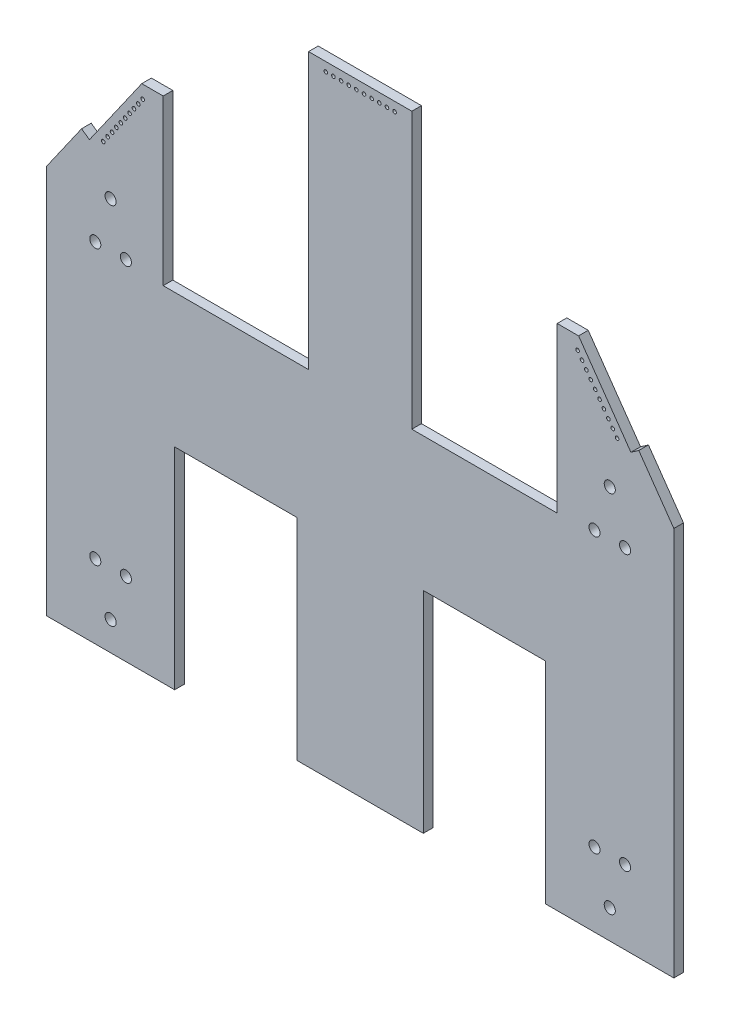
SolidWorks part; units mm, degrees
ref_plane "Front Plane" through (0, 0, 0) normal (0, 0, 1) x (1, 0, 0)
ref_plane "Top Plane" through (0, 0, 0) normal (0, 1, 0) x (1, 0, 0)
ref_plane "Right Plane" through (0, 0, 0) normal (1, 0, 0) x (0, 0, -1)
sketch "Sketch1" plane through (0, 0, 0) normal (0, 0, 1) x (1, 0, 0)
  line L0 (-19.3675, 84.4165) -> (-15.8104, 84.4165)
  line L1 (-5.817, 72.934) -> (-7.1277, 72.0162)
  line L2 (-5.817, 72.934) -> (0, 64.6264)
  line L3 (-15.8104, 84.4165) -> (-7.1277, 72.0162)
  line L4 (-62.5475, 0) -> (-62.5475, 34.925)
  line L5 (-62.5475, 34.925) -> (-82.8675, 34.925)
  line L6 (-82.8675, 34.925) -> (-82.8675, 0)
  line L7 (-21.2725, 34.925) -> (-21.2725, 0)
  line L8 (-41.5925, 34.925) -> (-21.2725, 34.925)
  line L9 (-41.5925, 0) -> (-41.5925, 34.925)
  line L10 (-82.8675, 0) -> (-104.14, 0)
  line L11 (-41.5925, 0) -> (-62.5475, 0)
  line L12 (-84.7725, 84.4165) -> (-84.7725, 57.15)
  line L13 (-84.7725, 57.15) -> (-60.6425, 57.15)
  line L14 (-60.6425, 57.15) -> (-60.6425, 102.87)
  line L18 (-43.4975, 102.87) -> (-60.6425, 102.87)
  line L24 (-43.4975, 102.87) -> (-43.4975, 57.15)
  line L25 (-43.4975, 57.15) -> (-19.3675, 57.15)
  line L26 (-19.3675, 57.15) -> (-19.3675, 84.4165)
  line L95 (0, 0) -> (0, 64.6264)
  line L96 (-104.14, 0) -> (-104.14, 64.6264)
  line L97 (0, 0) -> (-21.2725, 0)
  line L98 (-88.3296, 84.4165) -> (-97.0123, 72.0162)
  line L99 (-84.7725, 84.4165) -> (-88.3296, 84.4165)
  line L100 (-98.323, 72.934) -> (-97.0123, 72.0162)
  line L101 (-98.323, 72.934) -> (-104.14, 64.6264)
  line L299 (-52.07, 102.87) -> (-52.07, 0) construction
  dimension "D2" = 21.2725
  dimension "D5" = 104.14
  dimension "D6" = 82.8675
  dimension "D7" = 34.925
  dimension "D8" = 145
  dimension "D9" = 5.817
  dimension "D10" = 1.6
  dimension "D3" = 41.5925
  dimension "D4" = 62.5475
  dimension "D11" = 7.1277
  dimension "D12" = 15.8104
  dimension "D13" = 19.3675
  dimension "D14" = 19.3675
  dimension "D15" = 43.4975
  dimension "D16" = 57.15
  dimension "D17" = 84.4165
  dimension "D18" = 72.0162
  dimension "D19" = 72.934
  dimension "D20" = 64.6264
  dimension "D21" = 102.87
extrude "Boss-Extrude1" add sketch "Sketch1" along normal blind 1.6
sketch "Sketch2" plane through (0, 0, 0) normal (0, 0, -1) x (-1, 0, 0)
  line L1 (62.1596, 26.0248) -> (-24.5974, 26.0248)
  line L2 (62.1596, 26.0248) -> (62.1596, 63.281)
  line L3 (62.1596, 63.281) -> (-24.5974, 63.281)
  line L4 (-24.5974, 26.0248) -> (-24.5974, 63.281)
  arc A0 (-27.1374, 26.0248) -> (-24.5974, 23.4848) centre (-24.5974, 26.0248) ccw construction
ref_plane "Plane1" through (-52.07, 0, 0) normal (-1, 0, 0) x (0, 0, 1)
sketch "Sketch3" plane through (0, 0, 1.6) normal (0, 0, 1) x (1, 0, 0)
  line L0 (-92.7164, 4.9421) -> (-94.2912, 4.6373) construction
  line L1 (-94.2912, 4.9421) -> (-92.7164, 4.6373) construction
  line L2 (-95.2564, 12.4097) -> (-96.8312, 12.1049) construction
  line L3 (-96.8312, 12.4097) -> (-95.2564, 12.1049) construction
  line L4 (-92.7164, 4.9421) -> (-94.2912, 4.9421)
  line L5 (-92.7164, 4.6373) -> (-92.7164, 4.9421)
  line L6 (-94.2912, 4.6373) -> (-92.7164, 4.6373)
  line L7 (-94.2912, 4.9421) -> (-94.2912, 4.6373)
  line L8 (-92.7164, 4.9421) -> (-94.2912, 4.9421)
  line L9 (-92.7164, 4.6373) -> (-92.7164, 4.9421)
  line L10 (-94.2912, 4.6373) -> (-92.7164, 4.6373)
  line L11 (-94.2912, 4.9421) -> (-94.2912, 4.6373)
  line L12 (-91.7512, 12.4097) -> (-90.1764, 12.1049) construction
  line L13 (-91.7512, 12.1049) -> (-90.1764, 12.4097) construction
  line L14 (-91.7512, 12.1049) -> (-90.1764, 12.1049)
  line L15 (-91.7512, 12.4097) -> (-91.7512, 12.1049)
  line L16 (-90.1764, 12.4097) -> (-91.7512, 12.4097)
  line L17 (-90.1764, 12.1049) -> (-90.1764, 12.4097)
  line L18 (-91.7512, 12.1049) -> (-90.1764, 12.1049)
  line L19 (-91.7512, 12.4097) -> (-91.7512, 12.1049)
  line L20 (-90.1764, 12.4097) -> (-91.7512, 12.4097)
  line L21 (-90.1764, 12.1049) -> (-90.1764, 12.4097)
  line L22 (-96.8312, 12.1049) -> (-95.2564, 12.1049)
  line L23 (-96.8312, 12.4097) -> (-96.8312, 12.1049)
  line L24 (-95.2564, 12.4097) -> (-96.8312, 12.4097)
  line L25 (-95.2564, 12.1049) -> (-95.2564, 12.4097)
  line L26 (-96.8312, 12.1049) -> (-95.2564, 12.1049)
  line L27 (-96.8312, 12.4097) -> (-96.8312, 12.1049)
  line L28 (-95.2564, 12.4097) -> (-96.8312, 12.4097)
  line L29 (-95.2564, 12.1049) -> (-95.2564, 12.4097)
  line L30 (-95.2564, 57.9751) -> (-96.8312, 57.9751) construction
  line L31 (-95.2564, 57.9751) -> (-95.2564, 57.6703) construction
  line L32 (-96.8312, 57.6703) -> (-95.2564, 57.6703) construction
  line L33 (-96.8312, 57.6703) -> (-96.8312, 57.9751) construction
  line L34 (-90.1764, 57.9751) -> (-91.7512, 57.9751) construction
  line L35 (-90.1764, 57.9751) -> (-90.1764, 57.6703) construction
  line L36 (-91.7512, 57.6703) -> (-90.1764, 57.6703) construction
  line L37 (-91.7512, 57.6703) -> (-91.7512, 57.9751) construction
  line L38 (-94.2912, 65.1379) -> (-92.7164, 65.1379) construction
  line L39 (-94.2912, 65.1379) -> (-94.2912, 65.4427) construction
  line L40 (-92.7164, 65.4427) -> (-94.2912, 65.4427) construction
  line L41 (-92.7164, 65.4427) -> (-92.7164, 65.1379) construction
  line L42 (-95.2564, 57.9751) -> (-96.8312, 57.9751)
  line L43 (-95.2564, 57.9751) -> (-95.2564, 57.6703)
  line L44 (-96.8312, 57.6703) -> (-95.2564, 57.6703)
  line L45 (-96.8312, 57.6703) -> (-96.8312, 57.9751)
  line L46 (-90.1764, 57.9751) -> (-91.7512, 57.9751)
  line L47 (-90.1764, 57.9751) -> (-90.1764, 57.6703)
  line L48 (-91.7512, 57.6703) -> (-90.1764, 57.6703)
  line L49 (-91.7512, 57.6703) -> (-91.7512, 57.9751)
  line L50 (-94.2912, 65.1379) -> (-92.7164, 65.1379)
  line L51 (-94.2912, 65.1379) -> (-94.2912, 65.4427)
  line L52 (-92.7164, 65.4427) -> (-94.2912, 65.4427)
  line L53 (-92.7164, 65.4427) -> (-92.7164, 65.1379)
  line L54 (-92.7164, 65.4427) -> (-94.2912, 65.1379) construction
  line L55 (-90.1764, 57.9751) -> (-91.7512, 57.6703) construction
  line L56 (-95.2564, 57.9751) -> (-96.8312, 57.6703) construction
  line L57 (-52.07, -0.88) -> (-52.07, 0.88) construction
  circle A0 centre (-93.5038, 4.7897) radius 0.9207
  circle A1 centre (-90.9638, 12.2573) radius 0.9207
  circle A2 centre (-90.9638, 57.8227) radius 0.9207
  circle A3 centre (-96.0438, 12.2573) radius 0.9207
  circle A4 centre (-93.5038, 65.2903) radius 0.9207
  circle A5 centre (-96.0438, 57.8227) radius 0.9208
  circle A6 centre (-10.6363, 4.7897) radius 0.9207
  circle A7 centre (-8.0963, 12.2573) radius 0.9207
  circle A8 centre (-13.1763, 12.2573) radius 0.9207
  circle A9 centre (-8.0963, 57.8227) radius 0.9208
  circle A10 centre (-10.6363, 65.2903) radius 0.9207
  circle A11 centre (-13.1763, 57.8227) radius 0.9207
  point P2 (-93.5038, 4.7897)
  point P19 (-96.0438, 12.2573)
  point P20 (-90.9638, 12.2573)
  dimension "D2" = 1.8415
  dimension "D1" = 0
  dimension "D3" = 0
  dimension "D4" = 0
extrude "Cut-Extrude1" cut sketch "Sketch3" against normal blind 2.54 contours A3 | A1 | A0 | A4 | A2 | A5 | A11 | A9 | A8 | A7 | A6 | A10
sketch "Sketch4" plane through (0, 0, 0) normal (0, 0, -1) x (-1, 0, 0)
  line L0 (46.43, 101.445) -> (46.28, 101.295) construction
  line L1 (88.1846, 82.3606) -> (88.1477, 82.1517) construction
  line L2 (52.07, -0.88) -> (52.07, 0.88) construction
  line L3 (15.9554, 82.3606) -> (15.9923, 82.1517) construction
  line L4 (46.28, 101.295) -> (46.43, 101.295)
  line L5 (46.43, 101.295) -> (46.43, 101.445)
  line L6 (46.43, 101.445) -> (46.28, 101.445)
  line L7 (46.28, 101.445) -> (46.28, 101.295)
  line L8 (46.28, 101.295) -> (46.43, 101.295)
  line L9 (46.43, 101.295) -> (46.43, 101.445)
  line L10 (46.43, 101.445) -> (46.28, 101.445)
  line L11 (46.28, 101.445) -> (46.28, 101.295)
  line L12 (15.9554, 82.3606) -> (16.0783, 82.2746)
  line L13 (88.0617, 82.2746) -> (88.1477, 82.1517)
  line L14 (88.1477, 82.1517) -> (88.2706, 82.2377)
  line L15 (88.2706, 82.2377) -> (88.1846, 82.3606)
  line L16 (88.1846, 82.3606) -> (88.0617, 82.2746)
  line L17 (88.0617, 82.2746) -> (88.1477, 82.1517)
  line L18 (88.1477, 82.1517) -> (88.2706, 82.2377)
  line L19 (88.2706, 82.2377) -> (88.1846, 82.3606)
  line L20 (88.1846, 82.3606) -> (88.0617, 82.2746)
  line L21 (15.8694, 82.2377) -> (15.9554, 82.3606)
  line L22 (15.9923, 82.1517) -> (15.8694, 82.2377)
  line L23 (16.0783, 82.2746) -> (15.9923, 82.1517)
  circle A0 centre (46.355, 101.37) radius 0.3
  circle A1 centre (47.625, 101.37) radius 0.3
  circle A2 centre (48.895, 101.37) radius 0.3
  circle A3 centre (50.165, 101.37) radius 0.3
  circle A4 centre (51.435, 101.37) radius 0.3
  circle A5 centre (52.705, 101.37) radius 0.3
  circle A6 centre (53.975, 101.37) radius 0.3
  circle A7 centre (55.245, 101.37) radius 0.3
  circle A8 centre (56.515, 101.37) radius 0.3
  circle A9 centre (57.785, 101.37) radius 0.3
  circle A10 centre (88.1661, 82.2561) radius 0.3
  circle A11 centre (88.8946, 81.2158) radius 0.3
  circle A12 centre (89.623, 80.1755) radius 0.3
  circle A13 centre (90.3515, 79.1352) radius 0.3
  circle A14 centre (91.0799, 78.0948) radius 0.3
  circle A15 centre (91.8083, 77.0545) radius 0.3
  circle A16 centre (92.5368, 76.0142) radius 0.3
  circle A17 centre (93.2652, 74.9739) radius 0.3
  circle A18 centre (93.9937, 73.9336) radius 0.3
  circle A19 centre (94.7221, 72.8932) radius 0.3
  circle A20 centre (9.4179, 72.8932) radius 0.3
  circle A21 centre (10.1463, 73.9336) radius 0.3
  circle A22 centre (10.8748, 74.9739) radius 0.3
  circle A23 centre (11.6032, 76.0142) radius 0.3
  circle A24 centre (12.3317, 77.0545) radius 0.3
  circle A25 centre (13.0601, 78.0948) radius 0.3
  circle A26 centre (13.7885, 79.1352) radius 0.3
  circle A27 centre (14.517, 80.1755) radius 0.3
  circle A28 centre (15.2454, 81.2158) radius 0.3
  circle A29 centre (15.9739, 82.2561) radius 0.3
  dimension "D2" = 0.6
  dimension "D5" = 10
  dimension "D6" = 0.6
  dimension "D7" = 1.27
  dimension "D8" = 1.27
  dimension "D1" = 0
  dimension "D4" = 0
  dimension "D3" = 10
extrude "Cut-Extrude2" cut sketch "Sketch4" against normal blind 2.54 contours A0 | A1 | A2 | A9 | A8 | A7 | A6 | A5 | A4 | A3 | A19 | A18 | A17 | A16 | A15 | A14 | A13 | A12 | A11 | A10 | A20 | A21 | A22 | A23 | A24 | A25 | A26 | A27 | A28 | A29
